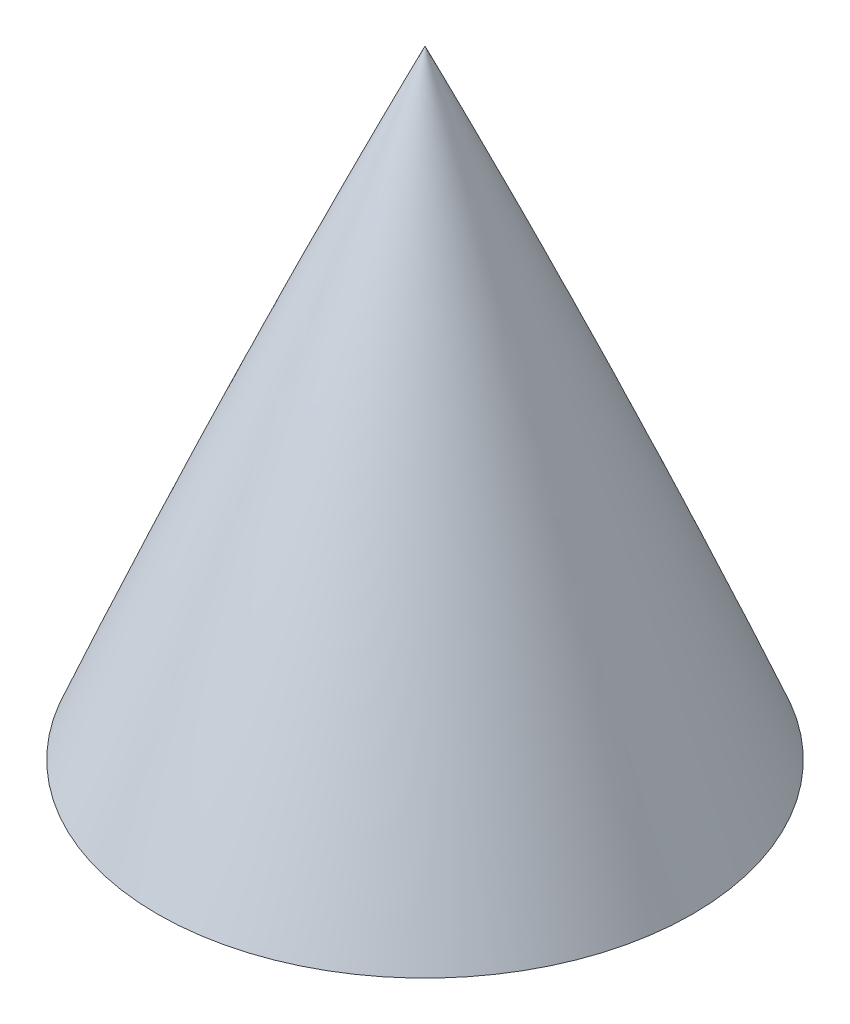
SolidWorks part; units mm, degrees
material "PVB"
ref_plane "Front Plane" through (0, 0, 0) normal (0, 0, 1) x (1, 0, 0)
ref_plane "Top Plane" through (0, 0, 0) normal (0, 1, 0) x (1, 0, 0)
ref_plane "Right Plane" through (0, 0, 0) normal (1, 0, 0) x (0, 0, -1)
sketch "Sketch2" plane through (0, 0, 0) normal (0, 0, 1) x (1, 0, 0)
  line L0 (0, 0) -> (0, 381) construction
  line L1 (-98.425, 0) -> (-90.551, 0)
  line L2 (0, 381) -> (0, 375.92)
  line L3 (0, 375.92) -> (0, 0)
  line L4 (0, 0) -> (-90.551, 0)
  arc A0 (0, 381) -> (-98.425, 0) centre (992.1135, -78.5092) ccw
  dimension "D1" = 381
  dimension "D2" = 5.08
  dimension "D3" = 98.425
  dimension "D4" = 7.874
revolve "Revolve1" add sketch "Sketch2" angle 360 about L2
sketch "Sketch3" plane through (0, 0, 0) normal (0, -1, 0) x (1, 0, 0)
  circle A0 centre (0, 0) radius 88.9
  circle A1 centre (0, 0) radius 86.995
  dimension "D1" = 177.8
extrude "Boss-Extrude1" [suppressed] add sketch "Sketch3" along normal blind 35.56
sketch "Sketch7" plane through (0, 0, 0) normal (0, -1, 0) x (1, 0, 0)
  circle A0 centre (-188.315, 83.0177) radius 421.4958
extrude "Cut-Extrude2" cut sketch "Sketch7" against normal blind 330.2
sketch "Sketch8" plane through (0, 330.2, 0) normal (0, -1, 0) x (-1, 0, 0)
  circle A0 centre (0, 0) radius 2.413
  dimension "D1" = 4.826
extrude "Cut-Extrude3" cut sketch "Sketch8" against normal blind 12.7
